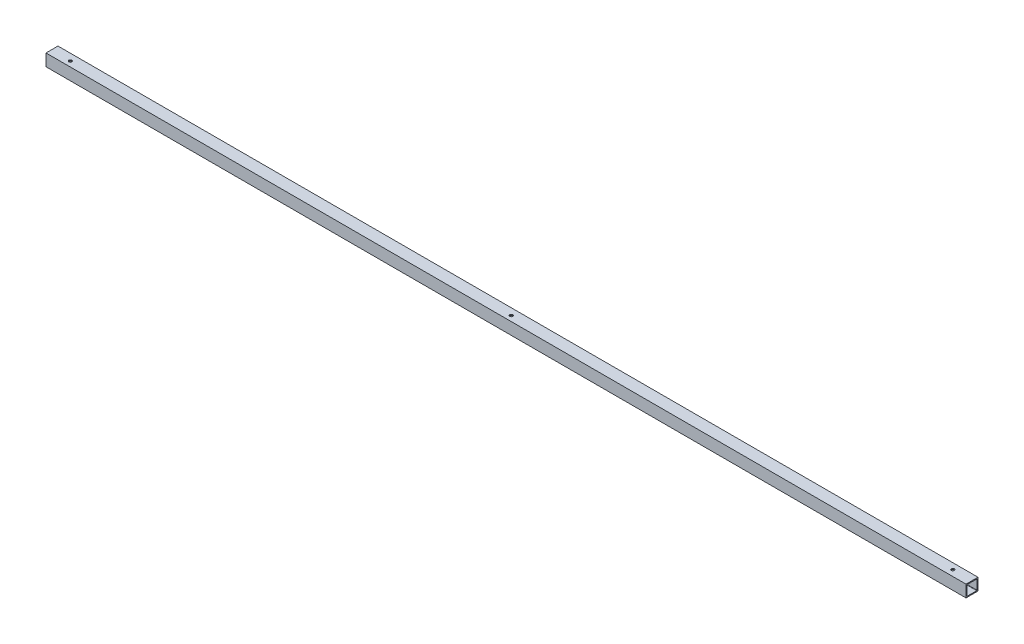
SolidWorks part; units mm, degrees
material "AISI 1035 Steel (SS)"
ref_plane "Front" through (0, 0, 0) normal (0, 0, 1) x (1, 0, 0)
ref_plane "Top" through (0, 0, 0) normal (0, 1, 0) x (1, 0, 0)
ref_plane "Right" through (0, 0, 0) normal (1, 0, 0) x (0, 0, -1)
sketch "Sketch1" plane through (0, 0, 0) normal (1, 0, 0) x (0, 0, -1)
  line L5 (0, 0) -> (15.875, 0)
  line L6 (0, 0) -> (0, 15.875)
  line L7 (0, 15.875) -> (15.875, 15.875)
  line L8 (15.875, 0) -> (15.875, 15.875)
  line L9 (1.7446, 1.2446) -> (14.1304, 1.2446)
  line L10 (1.2446, 1.7446) -> (1.2446, 14.1304)
  line L11 (1.7446, 14.6304) -> (14.1304, 14.6304)
  line L12 (14.6304, 1.7446) -> (14.6304, 14.1304)
  arc A0 (1.7446, 1.2446) -> (1.2446, 1.7446) centre (1.7446, 1.7446) cw
  arc A1 (14.1304, 1.2446) -> (14.6304, 1.7446) centre (14.1304, 1.7446) ccw
  arc A2 (14.1304, 14.6304) -> (14.6304, 14.1304) centre (14.1304, 14.1304) cw
  arc A3 (1.2446, 14.1304) -> (1.7446, 14.6304) centre (1.7446, 14.1304) cw
  point P10 (7.9375, 14.6304)
  point P11 (7.9375, 15.875)
  point P12 (1.2446, 7.9375)
  point P13 (0, 7.9375)
  point P18 (14.6304, 1.2446)
  point P21 (14.6304, 14.6304)
  dimension "D4" = 0.5
  dimension "D1" = 15.875
  dimension "D2" = 15.875
  dimension "D3" = 13.3858
extrude "Boss-Extrude1" add sketch "Sketch1" along normal blind 1219.2
sketch "Sketch2" plane through (0, 15.875, 0) normal (0, 1, 0) x (1, 0, 0)
  line L1 (0, 0) -> (0, 15.875) construction
  line L2 (1219.2, 15.875) -> (0, 15.875) construction
  line L3 (1219.2, 15.875) -> (1219.2, 0) construction
  line L4 (1193.8, 7.9375) -> (609.6005, 6.875) construction
  line L5 (609.6005, 6.875) -> (25.4, 6.875) construction
  circle A0 centre (609.6005, 6.875) radius 2
  circle A1 centre (25.4, 6.875) radius 2
  circle A4 centre (1193.8, 7.9375) radius 2
  dimension "D1" = 4
  dimension "D3" = 9
  dimension "D5" = 25.4
  dimension "D2" = 25.4
  dimension "D7" = 9
  dimension "D9" = 4
extrude "Cut-Extrude1" cut sketch "Sketch2" against normal through all
